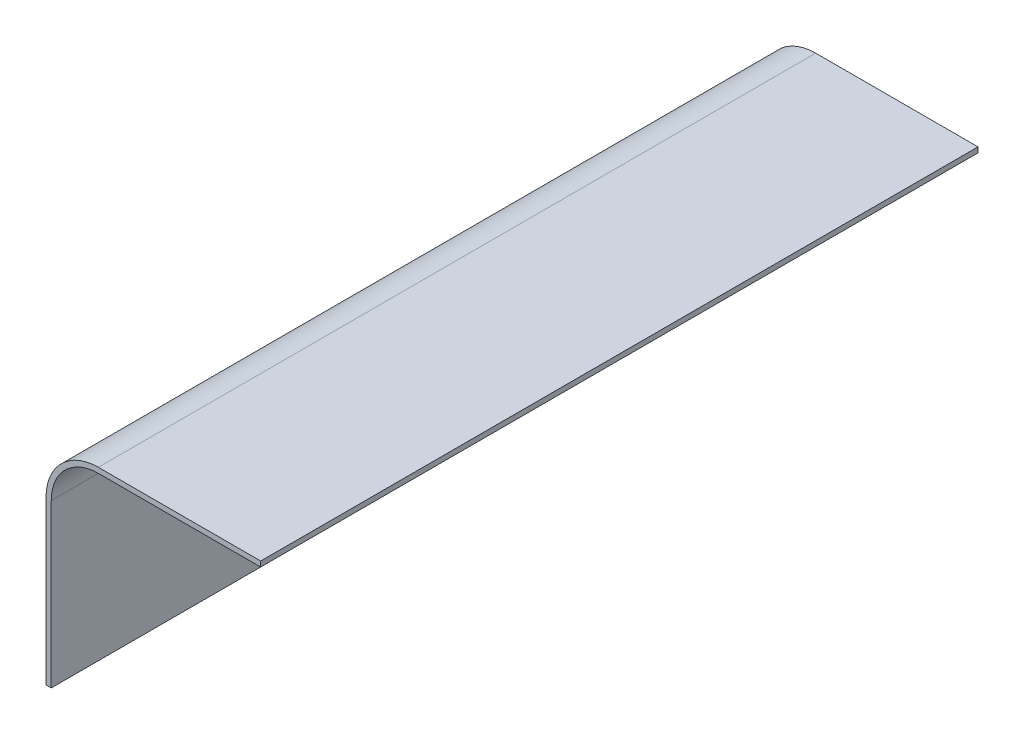
SolidWorks part; units mm, degrees
ref_plane "Front Plane" through (0, 0, 0) normal (0, 0, 1) x (1, 0, 0)
ref_plane "Top Plane" through (0, 0, 0) normal (0, 1, 0) x (1, 0, 0)
ref_plane "Right Plane" through (0, 0, 0) normal (1, 0, 0) x (0, 0, -1)
sketch "Sketch1" plane through (0, 0, 0) normal (0, 0, 1) x (1, 0, 0)
  line L0 (0, 0) -> (0, 62)
  line L1 (18, 80) -> (80, 80)
  line L2 (-2, 0) -> (-2, 62)
  line L3 (18, 82) -> (80, 82)
  line L4 (-2, 0) -> (0, 0)
  line L5 (80, 80) -> (80, 82)
  arc A0 (0, 62) -> (18, 80) centre (18, 62) cw
  arc A1 (-2, 62) -> (18, 82) centre (18, 62) cw
  dimension "D4" = 20
  dimension "D2" = 82
  dimension "D3" = 82
  dimension "D1" = 2
extrude "Boss-Extrude1" add sketch "Sketch1" against normal blind 274
